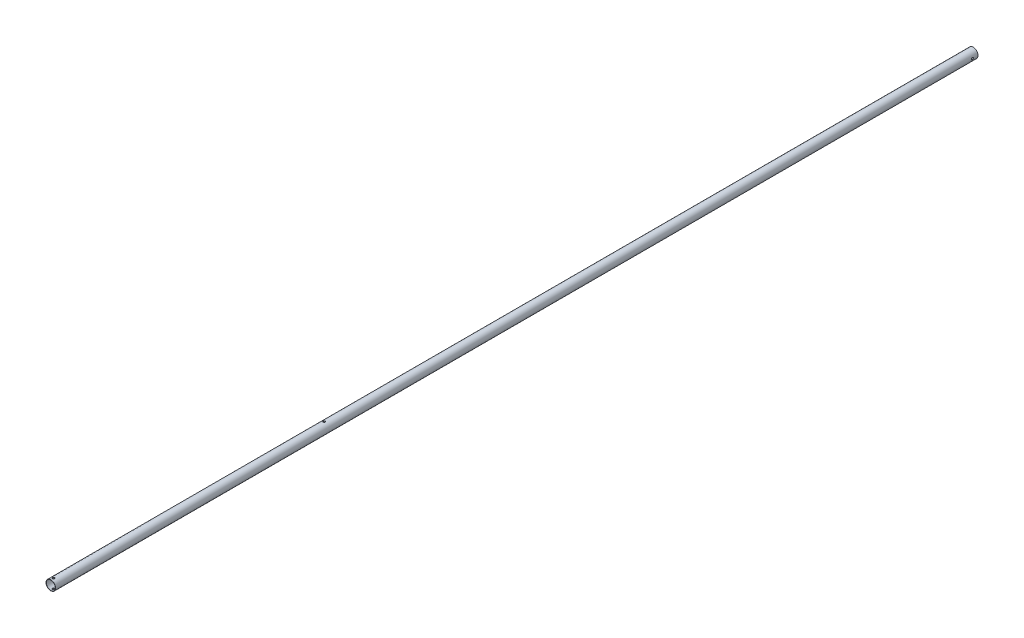
SolidWorks part; units mm, degrees
material "1060 Alloy"
ref_plane "Front Plane" through (0, 0, 0) normal (0, 0, 1) x (1, 0, 0)
ref_plane "Top Plane" through (0, 0, 0) normal (0, 1, 0) x (1, 0, 0)
ref_plane "Right Plane" through (0, 0, 0) normal (1, 0, 0) x (0, 0, -1)
sketch "Sketch1" plane through (0, 0, 0) normal (0, 0, 1) x (1, 0, 0)
  circle A0 centre (0, 0) radius 12.7
  circle A1 centre (0, 0) radius 11.9063
  dimension "D1" = 25.4
  dimension "D2" = 23.8125
extrude "Boss-Extrude1" add sketch "Sketch1" along normal blind 2443.8722
sketch "Sketch2" plane through (0, 0, 0) normal (0, 1, 0) x (1, 0, 0)
  line L0 (0, -2443.8722) -> (0, -2436.6222) construction
  line L1 (-12.7, -2443.8722) -> (12.7, -2443.8722) construction
  dimension "D1" = 7.25
hole_wizard "M5 Clearance Hole1" positions "Sketch3" profile "Sketch4" hole size "M5" standard "AS"
sketch "Sketch3" plane through (0, 0, 0) normal (0, 1, 0) x (1, 0, 0)
  point P0 (0, -2436.6222)
sketch "Sketch4" plane through (0, 0, 2436.6222) normal (1, 0, 0) x (0, 0, -1)
  line L0 (0, 0) -> (0, 12.7)
  line L1 (0, 12.7) -> (2.75, 12.7)
  line L2 (2.75, 12.7) -> (2.75, 0)
  line L5 (2.75, 0) -> (0, 0)
  line L11 (0, -6.35) -> (0, 107.95) construction
  dimension "Thru Hole Dia." = 5.5
  dimension "Thru Hole Depth" = 12.7
mirror "Mirror1" about plane through (0, 0, 0) normal (0, 1, 0) of "M5 Clearance Hole1"
sketch "Sketch5" plane through (0, 0, 0) normal (1, 0, 0) x (0, 0, -1)
  line L0 (0, 0) -> (-15, 0) construction
  dimension "D1" = 15
hole_wizard "M5 Clearance Hole3" positions "Sketch11" profile "Sketch12" hole size "M5" standard "AS"
sketch "Sketch11" plane through (0, 0, 0) normal (1, 0, 0) x (0, 0, -1)
  point P0 (-15, 0)
sketch "Sketch12" plane through (0, 0, 15) normal (0, 1, 0) x (0, 0, 1)
  line L0 (0, 0) -> (0, 12.7)
  line L1 (0, 12.7) -> (2.75, 12.7)
  line L2 (2.75, 12.7) -> (2.75, 0)
  line L5 (2.75, 0) -> (0, 0)
  line L11 (0, -6.35) -> (0, 107.95) construction
  dimension "Thru Hole Dia." = 5.5
  dimension "Thru Hole Depth" = 12.7
mirror "Mirror3" about plane through (0, 0, 0) normal (1, 0, 0) of "M5 Clearance Hole3"
sketch "Sketch13" plane through (0, 0, 0) normal (0, 1, 0) x (1, 0, 0)
  circle A0 centre (-0.7398, -1718.7545) radius 2.75
extrude "Cut-Extrude1" cut sketch "Sketch13" against normal through all both and the other way through all
equation "\"keelOutDiameter\"= 1in"
equation "\"keelInDiameter\"= \"keelOutDiameter\" - 0.125in"
equation "\"frontBoltClearance\"= 7.25mm"
equation "\"betweenBoltsDistance\"= 20mm"
equation "\"D1@Sketch2\"=\"frontBoltClearance\""
equation "\"wingLength\"= 1.4m"
equation "\"frontTubeLength\"= \"wingLength\" / sin ( 34.95deg )"
equation "\"D1@Boss-Extrude1\"=\"frontTubeLength\""
equation "\"D1@Sketch1\"=\"keelOutDiameter\""
equation "\"D2@Sketch1\"=\"keelOutDiameter\"-0.0625in"
